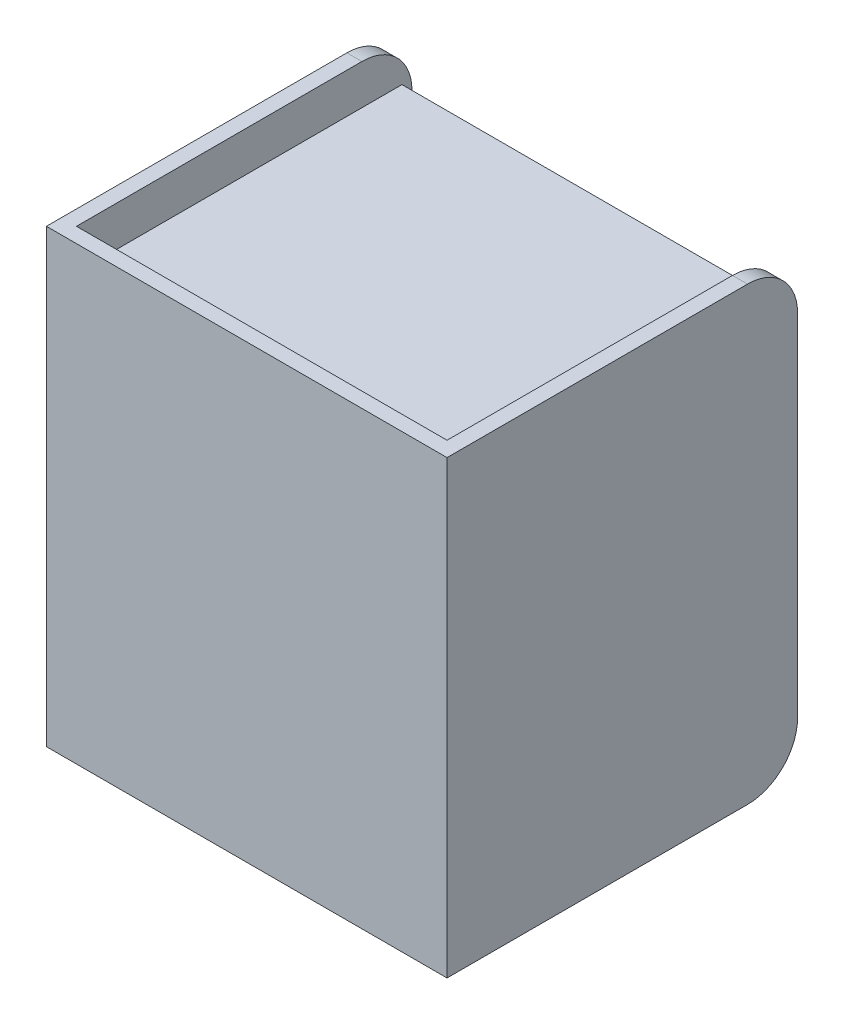
SolidWorks part; units mm, degrees
material "Oak"
ref_plane "Front Plane" through (0, 0, 0) normal (0, 0, 1) x (1, 0, 0)
ref_plane "Top Plane" through (0, 0, 0) normal (0, 1, 0) x (1, 0, 0)
ref_plane "Right Plane" through (0, 0, 0) normal (1, 0, 0) x (0, 0, -1)
sketch "Sketch1" plane through (0, 0, 0) normal (0, 0, 1) x (1, 0, 0)
  line L0 (-255.6602, 450) -> (-255.6602, 900) construction
  line L1 (-655.6602, 900) -> (144.3398, 900)
  line L2 (-655.6602, 900) -> (-655.6602, 0)
  line L3 (-655.6602, 0) -> (144.3398, 0)
  line L4 (144.3398, 900) -> (144.3398, 0)
  line L5 (-655.6602, 900) -> (144.3398, 0) construction
  line L6 (-655.6602, 0) -> (144.3398, 900) construction
  line L7 (-655.6602, 900) -> (-625.6602, 900)
  line L8 (-655.6602, 900) -> (-655.6602, 0)
  line L9 (-655.6602, 0) -> (-625.6602, 0)
  line L10 (-625.6602, 900) -> (-625.6602, 0)
  line L11 (144.3398, 0) -> (114.3398, 0)
  line L12 (114.3398, 900) -> (114.3398, 0)
  line L13 (144.3398, 900) -> (114.3398, 900)
  line L14 (144.3398, 900) -> (144.3398, 0)
  line L15 (-266.1102, 450) -> (-1179.071, 450) construction
  line L16 (-625.6602, 820) -> (114.3398, 820)
  line L17 (-625.6602, 820) -> (-625.6602, 790)
  line L18 (-625.6602, 790) -> (114.3398, 790)
  line L19 (114.3398, 820) -> (114.3398, 790)
  line L20 (-625.6602, 110) -> (114.3398, 110)
  line L21 (114.3398, 80) -> (114.3398, 110)
  line L22 (-625.6602, 80) -> (114.3398, 80)
  line L23 (-625.6602, 80) -> (-625.6602, 110)
  line L25 (-625.6602, 465) -> (114.3398, 465)
  line L26 (-625.6602, 465) -> (-625.6602, 435)
  line L27 (-625.6602, 435) -> (114.3398, 435)
  line L28 (114.3398, 465) -> (114.3398, 435)
  line L29 (-625.6602, 465) -> (114.3398, 435) construction
  line L30 (-625.6602, 435) -> (114.3398, 465) construction
  point P0 (-255.6602, 450)
  point P26 (-255.6602, 450)
  dimension "D1" = 900
  dimension "D2" = 800
  dimension "D3" = 30
  dimension "D4" = 30
  dimension "D5" = 80
  dimension "D6" = 80
  dimension "D7" = 30
sketch "Sketch2" plane through (0, 0, 0) normal (0, 0, 1) x (1, 0, 0)
  line L1 (-655.6602, 900) -> (-625.6602, 900)
  line L2 (-655.6602, 900) -> (-655.6602, 0)
  line L3 (-655.6602, 0) -> (-625.6602, 0)
  line L4 (-625.6602, 900) -> (-625.6602, 0)
  line L5 (-655.6602, 900) -> (-625.6602, 0) construction
  line L6 (-655.6602, 0) -> (-625.6602, 900) construction
  line L7 (144.3398, 0) -> (114.3398, 0)
  line L8 (144.3398, 0) -> (144.3398, 900)
  line L9 (144.3398, 900) -> (114.3398, 900)
  line L10 (114.3398, 0) -> (114.3398, 900)
  line L11 (144.3398, 0) -> (114.3398, 900) construction
  line L12 (144.3398, 900) -> (114.3398, 0) construction
  point P4 (-640.6602, 450)
  point P11 (129.3398, 450)
extrude "Boss-Extrude1" add sketch "Sketch2" along normal blind 700
sketch "Sketch3" plane through (0, 0, 700) normal (0, 0, 1) x (1, 0, 0)
  line L1 (-625.6602, 900) -> (114.3398, 900)
  line L2 (-625.6602, 900) -> (-625.6602, 0)
  line L3 (-625.6602, 0) -> (114.3398, 0)
  line L4 (114.3398, 900) -> (114.3398, 0)
  line L5 (-625.6602, 900) -> (114.3398, 0) construction
  line L6 (-625.6602, 0) -> (114.3398, 900) construction
  point P4 (-255.6602, 450)
extrude "Boss-Extrude2" add sketch "Sketch3" against normal blind 30 separate body
sketch "Sketch4" plane through (0, 0, 670) normal (0, 0, -1) x (-1, 0, 0)
  line L1 (-114.3398, 820) -> (625.6602, 820)
  line L2 (-114.3398, 820) -> (-114.3398, 790)
  line L3 (-114.3398, 790) -> (625.6602, 790)
  line L4 (625.6602, 820) -> (625.6602, 790)
  line L5 (-114.3398, 820) -> (625.6602, 790) construction
  line L6 (-114.3398, 790) -> (625.6602, 820) construction
  line L7 (-114.3398, 110) -> (625.6602, 110)
  line L8 (-114.3398, 110) -> (-114.3398, 80)
  line L9 (-114.3398, 80) -> (625.6602, 80)
  line L10 (625.6602, 110) -> (625.6602, 80)
  line L11 (-114.3398, 110) -> (625.6602, 80) construction
  line L12 (-114.3398, 80) -> (625.6602, 110) construction
  point P4 (255.6602, 805)
  point P11 (255.6602, 95)
extrude "Boss-Extrude3" add sketch "Sketch4" along normal blind 650
sketch "Sketch5" plane through (0, 0, 670) normal (0, 0, -1) x (-1, 0, 0)
  line L1 (-114.3398, 465) -> (625.6602, 465)
  line L2 (-114.3398, 465) -> (-114.3398, 435)
  line L3 (-114.3398, 435) -> (625.6602, 435)
  line L4 (625.6602, 465) -> (625.6602, 435)
  line L5 (-114.3398, 465) -> (625.6602, 435) construction
  line L6 (-114.3398, 435) -> (625.6602, 465) construction
  point P4 (255.6602, 450)
extrude "Boss-Extrude4" add sketch "Sketch5" along normal blind 620
fillet "Fillet1" radius 100 4 edges at (129.3398, 0, 0) (-640.6602, 0, 0) (-640.6602, 900, 0) (129.3398, 900, 0)
sketch "Sketch7" plane through (0, 0, 20) normal (0, 0, -1) x (-1, 0, 0)
  line L0 (625.6602, 100) -> (625.6602, 800) construction
  line L1 (-114.3398, 790) -> (625.6602, 790)
  line L2 (-114.3398, 790) -> (-114.3398, 465)
  line L3 (-114.3398, 465) -> (625.6602, 465)
  line L4 (625.6602, 790) -> (625.6602, 465)
  line L5 (-114.3398, 790) -> (625.6602, 465) construction
  line L6 (-114.3398, 465) -> (625.6602, 790) construction
  point P4 (255.6602, 627.5)
  dimension "D1" = 325
extrude "Boss-Extrude7" add sketch "Sketch7" against normal blind 20
sketch "Sketch8" plane through (0, 0, 20) normal (0, 0, -1) x (-1, 0, 0)
  line L1 (-114.3398, 110) -> (625.6602, 110)
  line L2 (-114.3398, 110) -> (-114.3398, 435)
  line L3 (-114.3398, 435) -> (625.6602, 435)
  line L4 (625.6602, 110) -> (625.6602, 435)
  line L5 (-114.3398, 110) -> (625.6602, 435) construction
  line L6 (-114.3398, 435) -> (625.6602, 110) construction
  point P4 (255.6602, 272.5)
extrude "Boss-Extrude8" add sketch "Sketch8" against normal blind 20
sketch "Sketch9" plane through (0, 0, 20) normal (0, 0, -1) x (-1, 0, 0)
  line L0 (625.6602, 465) -> (625.6602, 820) construction
  line L1 (625.6602, 465) -> (-114.3398, 465) construction
  circle A0 centre (525.6602, 645) radius 20
  dimension "D1" = 100
  dimension "D2" = 180
extrude "Boss-Extrude9" add sketch "Sketch9" along normal blind 25 separate body
sketch "Sketch10" plane through (0, 0, -5) normal (0, 0, -1) x (-1, 0, 0)
  circle A0 centre (525.6602, 645) radius 25
  dimension "D1" = 50
extrude "Boss-Extrude10" add sketch "Sketch10" along normal blind 20
fillet "Fillet2" radius 15 1 edges at (-550.6602, 645, -25)
pattern_linear "LPattern3" count 2 spacing 350 along (0, -1, 0) of "Boss-Extrude9", "Boss-Extrude10"
sketch "Sketch12" plane through (0, 0, -5) normal (0, 0, -1) x (-1, 0, 0)
  circle A0 centre (525.6602, 295) radius 25
  circle A1 centre (525.6602, 295) radius 20 construction
  dimension "D1" = 50
extrude "Boss-Extrude11" add sketch "Sketch12" along normal blind 20
fillet "Fillet3" radius 15 1 edges at (-550.6602, 295, -25)
sketch "Sketch13" plane through (0, 0, 20) normal (0, 0, -1) x (-1, 0, 0)
  line L0 (-114.3398, 820) -> (-114.3398, 465) construction
  line L1 (625.6602, 465) -> (-114.3398, 465) construction
  circle A0 centre (-14.3398, 645) radius 20
  dimension "D1" = 100
  dimension "D2" = 180
extrude "Boss-Extrude12" add sketch "Sketch13" along normal blind 25
sketch "Sketch14" plane through (0, 0, -5) normal (0, 0, -1) x (-1, 0, 0)
  circle A0 centre (-14.3398, 645) radius 30
extrude "Boss-Extrude13" add sketch "Sketch14" along normal blind 20
fillet "Fillet4" radius 15 1 edges at (-15.6602, 645, -25)
pattern_linear "LPattern4" count 2 spacing 350 along (0, -1, 0) of "Fillet4", "Boss-Extrude13", "Boss-Extrude12"
